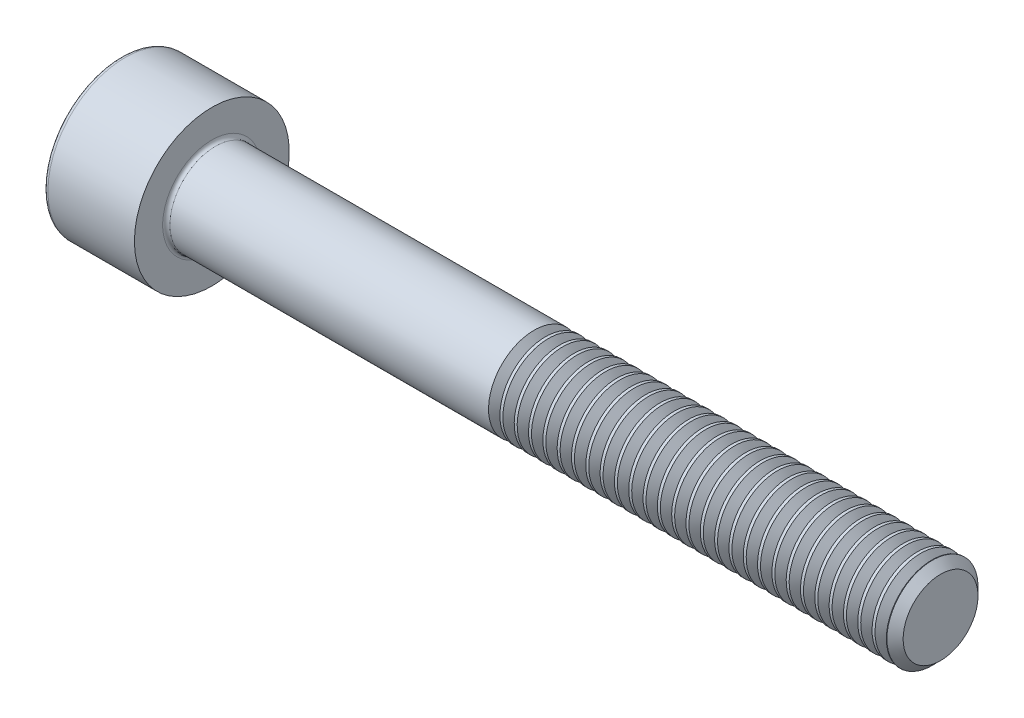
SolidWorks part; units mm, degrees
revolve "Base-Revolve" add sketch "BodySke"
sketch "BodySke" plane through (0, 0, 0) normal (0, 0, 1) x (1, 0, 0)
  line L0 (0, 0) -> (0, 4.25)
  line L1 (0, 4.25) -> (5, 4.25)
  line L2 (5, 4.25) -> (5, 2.5)
  line L3 (5, 2.5) -> (44.555, 2.5)
  line L4 (45, 2.055) -> (45, 0)
  line L5 (45, 0) -> (0, 0)
  line L6 (-31.75, 0) -> (127, 0) construction
  line L8 (45, 2.055) -> (44.555, 2.5)
  line L10 (45, -2.055) -> (44.555, -2.5) construction
  line L11 (5.8, 9.525) -> (5.8, 3.175) construction
  line L12 (23, 9.525) -> (23, 3.175) construction
  line L13 (-15, 9.525) -> (-15, 3.175) construction
  dimension "Head_ht" = 5
  dimension "Length" = 40
  dimension "Body_ch_ang" = 45
  dimension "Diameter" = 5
  dimension "Minor_dia" = 4.11
  dimension "Advance" = 0.8
  dimension "Thread_nom" = 22
  dimension "Thread_length" = 60
  dimension "Head_dia" = 8.5
cosmetic thread "ThreadCosmetic" [suppressed]
fillet "Fillet1" radius 0.2 1 edges at (5, 0, 2.5)
fillet "Fillet2" radius 0.25 1 edges at (0, 0, 4.25)
ref_plane "Plane1" through (0, 0, 0) normal (0, 0, 1) x (1, 0, 0)
ref_plane "Plane2" through (0, 0, 0) normal (0, 1, 0) x (1, 0, 0)
ref_plane "Plane3" through (0, 0, 0) normal (1, 0, 0) x (0, 0, -1)
sketch "Sketch2" plane through (0, 0, 0) normal (0, 0, 1) x (1, 0, 0)
  line L0 (0, 2.042) -> (2.5, 2.042)
  line L1 (2.5, 2.042) -> (3.6789, 0)
  line L2 (-31.75, 0) -> (127, 0) construction
  line L3 (3.6789, 0) -> (0, 0)
  line L4 (0, 0) -> (0, 2.042)
  line L6 (0, 0) -> (47.625, 0) construction
  dimension "D1" = 2.042
  dimension "D2" = 60
  dimension "Depth" = 2.5
revolve "Hex-PreBroach" cut sketch "Sketch2" angle 360 about L6
sketch "Sketch3" plane through (0, 0, 0) normal (-1, 0, 0) x (0, 0.5, 0.866)
  line L0 (1.1789, 2.042) -> (-1.1789, 2.042)
  line L1 (-1.1789, 2.042) -> (-2.3579, 0)
  line L2 (1.1789, 2.042) -> (2.3579, 0)
  line L3 (1.1789, -2.042) -> (2.3579, 0)
  line L4 (1.1789, -2.042) -> (-1.1789, -2.042)
  line L5 (-1.1789, -2.042) -> (-2.3579, 0)
  dimension "D1" = 2.042
  dimension "D2" = 2.042
  dimension "Hex_size" = 4.084
extrude "Hex" cut sketch "Sketch3" against normal blind 2.5
sketch "ThdSchSke" plane through (0, 0, 0) normal (0, 0, 1) x (1, 0, 0)
  line L0 (23, -2.055) -> (22.6884, -2.5)
  line L1 (23, -2.055) -> (23.3116, -2.5)
  line L2 (23.3116, -2.5) -> (23.3116, -3.125)
  line L3 (-3.175, 0) -> (5.1513, 0) construction
  line L4 (0, 4) -> (0, -4) construction
  line L5 (23.3116, -3.125) -> (22.6884, -3.125)
  line L6 (22.6884, -3.125) -> (22.6884, -2.5)
  dimension "Thread_minor" = 4.11
  dimension "Diameter" = 5
  dimension "Start" = 23
revolve "ThreadSchematic" cut sketch "ThdSchSke" angle 360 about L3
pattern_linear "ThdSchPat" count 28 spacing 0.7857 along (1, 0, 0) of "ThreadSchematic"
equation "\"D2@Sketch3\" = \"Hex_size@Sketch3\" / 2"
equation "\"D1@Sketch3\" = \"Hex_size@Sketch3\" / 2"
equation "\"D1@Sketch2\" = \"Hex_size@Sketch3\" / 2"
equation "\"Thread_minor@ThreadCosmetic\"  =  \"Minor_dia@BodySke\""
equation "\"Depth@Sketch2\" =  \"Key_eng@Hex\""
equation "\"Thread_length@ThreadCosmetic\" = ((sgn( (\"Length@BodySke\" - \"Advance@BodySke\" * 3.0) - \"Thread_nom@BodySke\" )-1)*( (\"Length@BodySke\" - \"Advance@BodySke\" * 3.0) - \"Thread_nom@BodySke\" ))/-2+ \"Thread_nom@BodySke\""
equation "\"Thread_minor@ThdSchSke\" = \"Minor_dia@BodySke\""
equation "\"Diameter@ThdSchSke\" = \"Diameter@BodySke\""
equation "\"Overcut@ThdSchSke\" = \"Diameter@BodySke\" * 1.25"
equation "\"Start@ThdSchSke\" = \"Head_ht@BodySke\" + \"Length@BodySke\" - \"Thread_length@ThreadCosmetic\"  '---Non-countersunk---"
equation "\"Num_threads@ThdSchPat\" = int( \"Thread_length@ThreadCosmetic\" / \"Advance@BodySke\" + 0.999 )  + 1"
equation "\"Advance@ThdSchPat\" = \"Thread_length@ThreadCosmetic\" /  (\"Num_threads@ThdSchPat\" - 1) 'relax it"
equation "\"Num_threads@ThdSchPat\" = \"Num_threads@ThdSchPat\" - sgn( \"Num_threads@ThdSchPat\" - 1) '---chamfered tips only---"
